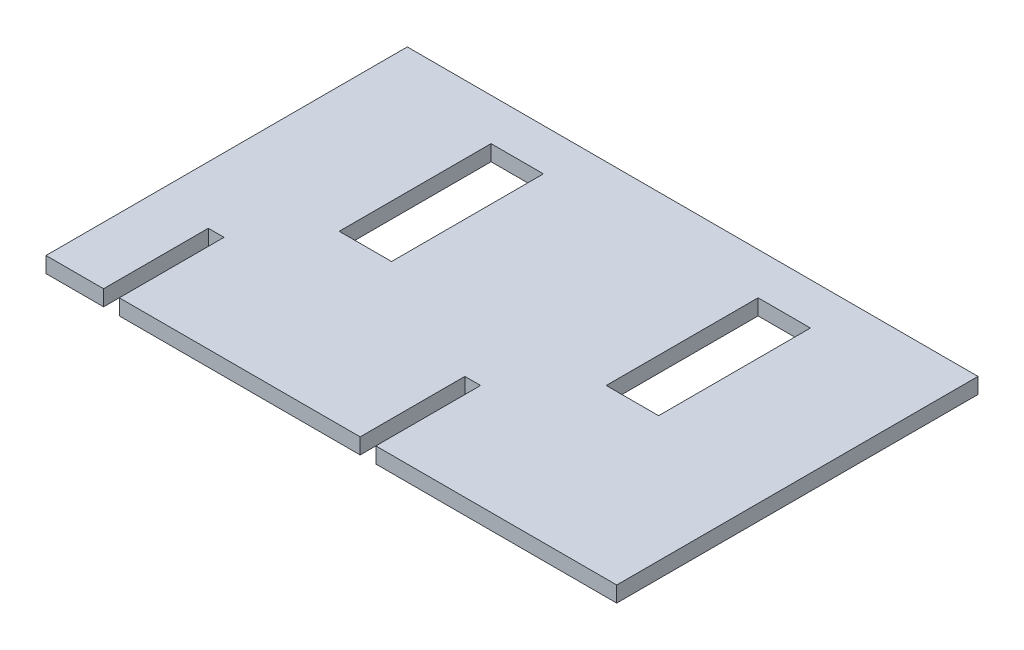
SolidWorks part; units mm, degrees
ref_plane "Front Plane" through (0, 0, 0) normal (0, 0, 1) x (1, 0, 0)
ref_plane "Top Plane" through (0, 0, 0) normal (0, 1, 0) x (1, 0, 0)
ref_plane "Right Plane" through (0, 0, 0) normal (1, 0, 0) x (0, 0, -1)
sketch "Sketch1" plane through (0, 0, 0) normal (0, 1, 0) x (1, 0, 0)
  line L1 (-27.25, 17.25) -> (27.25, 17.25)
  line L2 (-27.25, 17.25) -> (-27.25, -17.25)
  line L3 (-27.25, -17.25) -> (27.25, -17.25)
  line L4 (27.25, 17.25) -> (27.25, -17.25)
  line L5 (-27.25, 17.25) -> (27.25, -17.25) construction
  line L6 (-27.25, -17.25) -> (27.25, 17.25) construction
  point P0 (0, 0)
extrude "Boss-Extrude1" add sketch "Sketch1" along normal blind 1.5
sketch "Sketch2" plane through (0, 1.5, 0) normal (0, 1, 0) x (1, 0, 0)
  line L0 (0, 17.25) -> (0, 6)
  line L1 (27.25, 17.25) -> (-27.25, 17.25) construction
sketch "Sketch3" plane through (0, 1.5, 0) normal (0, 1, 0) x (1, 0, 0)
  line L0 (0, 6) -> (-27.25, 6)
  line L1 (-27.25, 17.25) -> (-27.25, -17.25) construction
sketch "Sketch5" plane through (0, 1.5, 0) normal (0, 1, 0) x (1, 0, 0)
  line L0 (-27.25, 6) -> (-12.75, 6)
sketch "Sketch6" plane through (0, 1.5, 0) normal (0, 1, 0) x (1, 0, 0)
  line L1 (-15.25, 13.25) -> (-10.25, 13.25)
  line L2 (-15.25, 13.25) -> (-15.25, -1.25)
  line L3 (-15.25, -1.25) -> (-10.25, -1.25)
  line L4 (-10.25, 13.25) -> (-10.25, -1.25)
  line L5 (-15.25, 13.25) -> (-10.25, -1.25) construction
  line L6 (-15.25, -1.25) -> (-10.25, 13.25) construction
  point P0 (-12.75, 6)
extrude "Cut-Extrude1" cut sketch "Sketch6" against normal blind 2
sketch "Sketch7" plane through (0, 1.5, 0) normal (0, 1, 0) x (1, 0, 0)
  line L0 (0, 6) -> (27.25, 6)
  line L1 (27.25, -17.25) -> (27.25, 17.25) construction
sketch "Sketch8" plane through (0, 1.5, 0) normal (0, 1, 0) x (1, 0, 0)
  line L0 (27.25, 6) -> (12.75, 6)
sketch "Sketch9" plane through (0, 1.5, 0) normal (0, 1, 0) x (1, 0, 0)
  line L1 (10.25, 13.25) -> (15.25, 13.25)
  line L2 (10.25, 13.25) -> (10.25, -1.25)
  line L3 (10.25, -1.25) -> (15.25, -1.25)
  line L4 (15.25, 13.25) -> (15.25, -1.25)
  line L5 (10.25, 13.25) -> (15.25, -1.25) construction
  line L6 (10.25, -1.25) -> (15.25, 13.25) construction
  point P0 (12.75, 6)
extrude "Cut-Extrude2" cut sketch "Sketch9" against normal blind 2
sketch "Sketch10" plane through (0, 1.5, 0) normal (0, 1, 0) x (1, 0, 0)
  line L0 (-27.25, -17.25) -> (-21.75, -17.25)
  line L1 (-27.25, -17.25) -> (27.25, -17.25) construction
sketch "Sketch11" plane through (0, 1.5, 0) normal (0, 1, 0) x (1, 0, 0)
  line L0 (-21.75, -17.25) -> (-20.25, -17.25)
  line L1 (-27.25, -17.25) -> (27.25, -17.25) construction
sketch "Sketch12" plane through (0, 1.5, 0) normal (0, 1, 0) x (1, 0, 0)
  line L0 (-20.25, -17.25) -> (2.75, -17.25)
  line L1 (-27.25, -17.25) -> (27.25, -17.25) construction
sketch "Sketch27" plane through (0, 1.5, 0) normal (0, 1, 0) x (1, 0, 0)
  line L0 (-21.75, -17.25) -> (-21.75, -7.25)
  line L1 (-21.75, -7.25) -> (-20.25, -7.25)
  line L2 (-20.25, -7.25) -> (-20.25, -17.25)
  line L3 (-20.25, -17.25) -> (-21.75, -17.25)
extrude "Cut-Extrude3" cut sketch "Sketch27" against normal blind 2
sketch "Sketch37" plane through (0, 1.5, 0) normal (0, 1, 0) x (1, 0, 0)
  line L0 (2.75, -17.25) -> (4.25, -17.25)
  line L1 (-20.25, -17.25) -> (27.25, -17.25) construction
  line L2 (2.75, -17.25) -> (2.75, -7.25)
  line L3 (2.75, -7.25) -> (4.25, -7.25)
  line L4 (4.25, -7.25) -> (4.25, -17.25)
extrude "Cut-Extrude10" cut sketch "Sketch37" against normal blind 2
